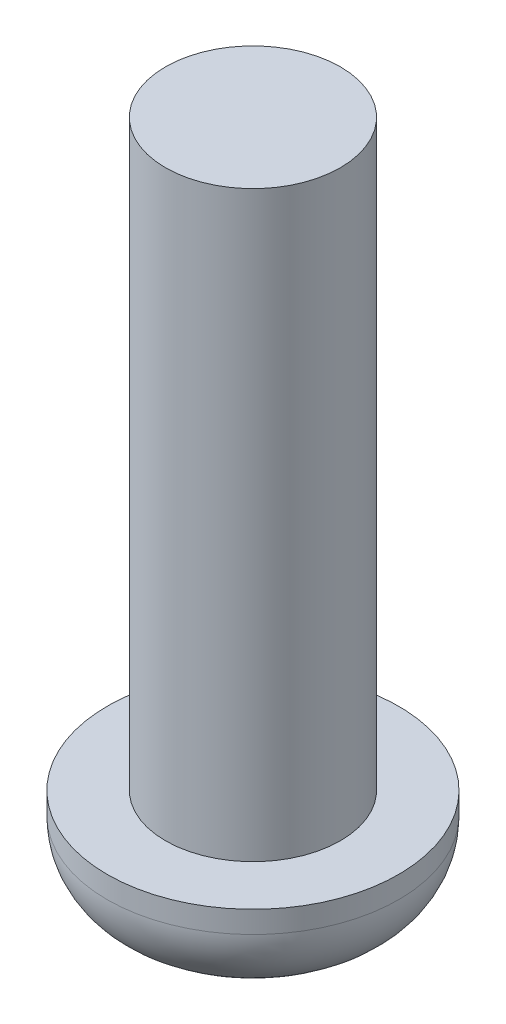
SolidWorks part; units mm, degrees
material "Plain Carbon Steel"
ref_plane "Front Plane" through (0, 0, 0) normal (0, 0, 1) x (1, 0, 0)
ref_plane "Top Plane" through (0, 0, 0) normal (0, 1, 0) x (1, 0, 0)
ref_plane "Right Plane" through (0, 0, 0) normal (1, 0, 0) x (0, 0, -1)
sketch "Sketch1" plane through (0, 0, 0) normal (0, 1, 0) x (1, 0, 0)
  circle A0 centre (0, 0) radius 4
  dimension "D1" = 8
extrude "Boss-Extrude1" add sketch "Sketch1" along normal blind 2.6
sketch "Sketch2" plane through (0, 2.6, 0) normal (0, 1, 0) x (1, 0, 0)
  circle A0 centre (0, 0) radius 2.4
  dimension "D1" = 4.8
extrude "Boss-Extrude2" add sketch "Sketch2" along normal blind 16
fillet "Fillet1" radius 2 1 edges at (0, 0, 4)
